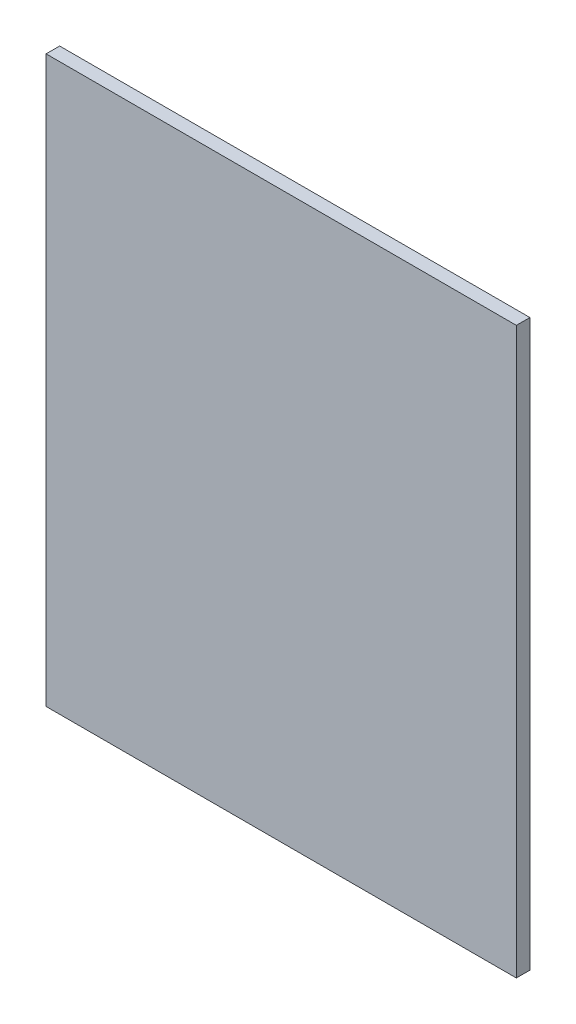
SolidWorks part; units mm, degrees
ref_plane "Plan de face" through (0, 0, 0) normal (0, 0, 1) x (1, 0, 0)
ref_plane "Plan de dessus" through (0, 0, 0) normal (0, 1, 0) x (1, 0, 0)
ref_plane "Plan de droite" through (0, 0, 0) normal (1, 0, 0) x (0, 0, -1)
sketch "Esquisse1" plane through (0, 0, 0) normal (0, 0, 1) x (1, 0, 0)
  line L1 (-120.1569, 126.1867) -> (87.8431, 126.1867)
  line L2 (-120.1569, 126.1867) -> (-120.1569, -123.8133)
  line L3 (-120.1569, -123.8133) -> (87.8431, -123.8133)
  line L4 (87.8431, 126.1867) -> (87.8431, -123.8133)
  dimension "D1" = 250
  dimension "D2" = 208
extrude "Boss.-Extru.1" add sketch "Esquisse1" along normal blind 6
